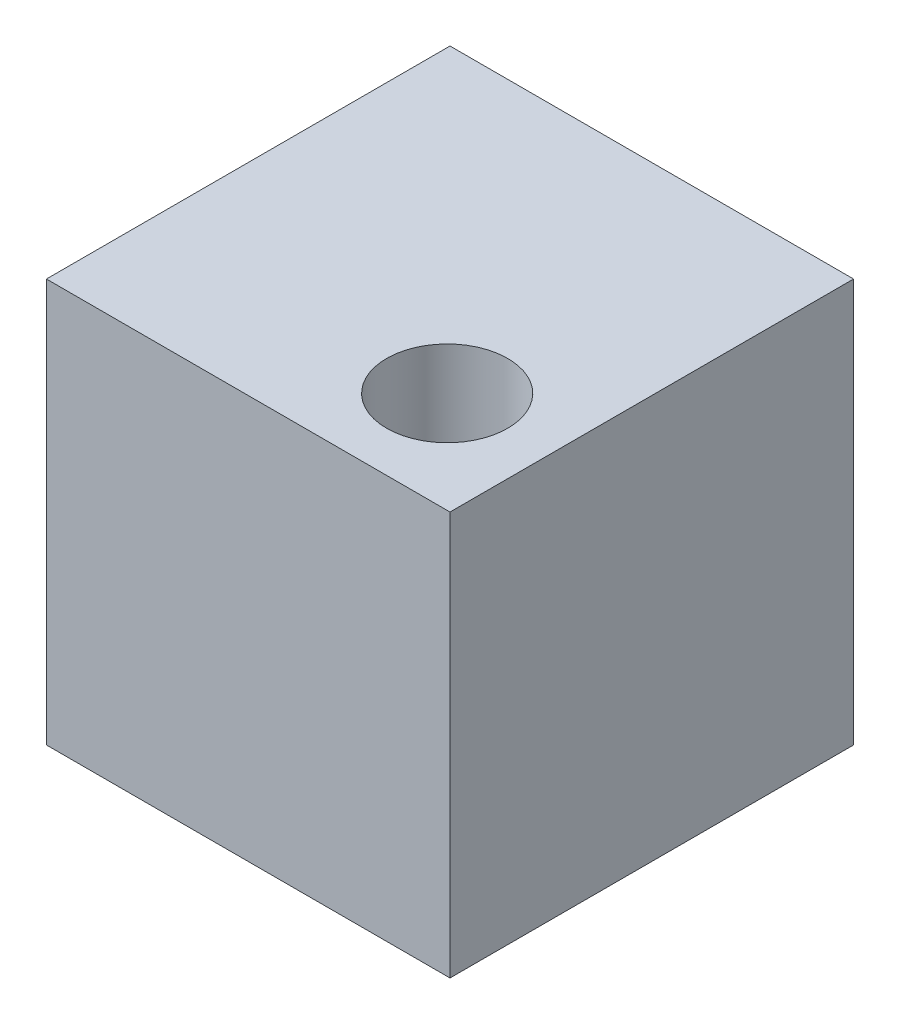
SolidWorks part; units mm, degrees
ref_plane "Front Plane" through (0, 0, 0) normal (0, 0, 1) x (1, 0, 0)
ref_plane "Top Plane" through (0, 0, 0) normal (0, 1, 0) x (1, 0, 0)
ref_plane "Right Plane" through (0, 0, 0) normal (1, 0, 0) x (0, 0, -1)
sketch "Sketch1" plane through (0, 0, 0) normal (0, 1, 0) x (1, 0, 0)
  line L1 (-3.6626, 2.1938) -> (6.3374, 2.1938)
  line L2 (-3.6626, 2.1938) -> (-3.6626, -7.8062)
  line L3 (-3.6626, -7.8062) -> (6.3374, -7.8062)
  line L4 (6.3374, 2.1938) -> (6.3374, -7.8062)
  dimension "D1" = 10
  dimension "D2" = 10
extrude "Boss-Extrude1" add sketch "Sketch1" along normal blind 10
sketch "Sketch2" plane through (0, 10, 0) normal (0, 1, 0) x (1, 0, 0)
  circle A0 centre (3.7563, -5.2952) radius 1.5
extrude "Cut-Extrude1" cut sketch "Sketch2" against normal blind 5
